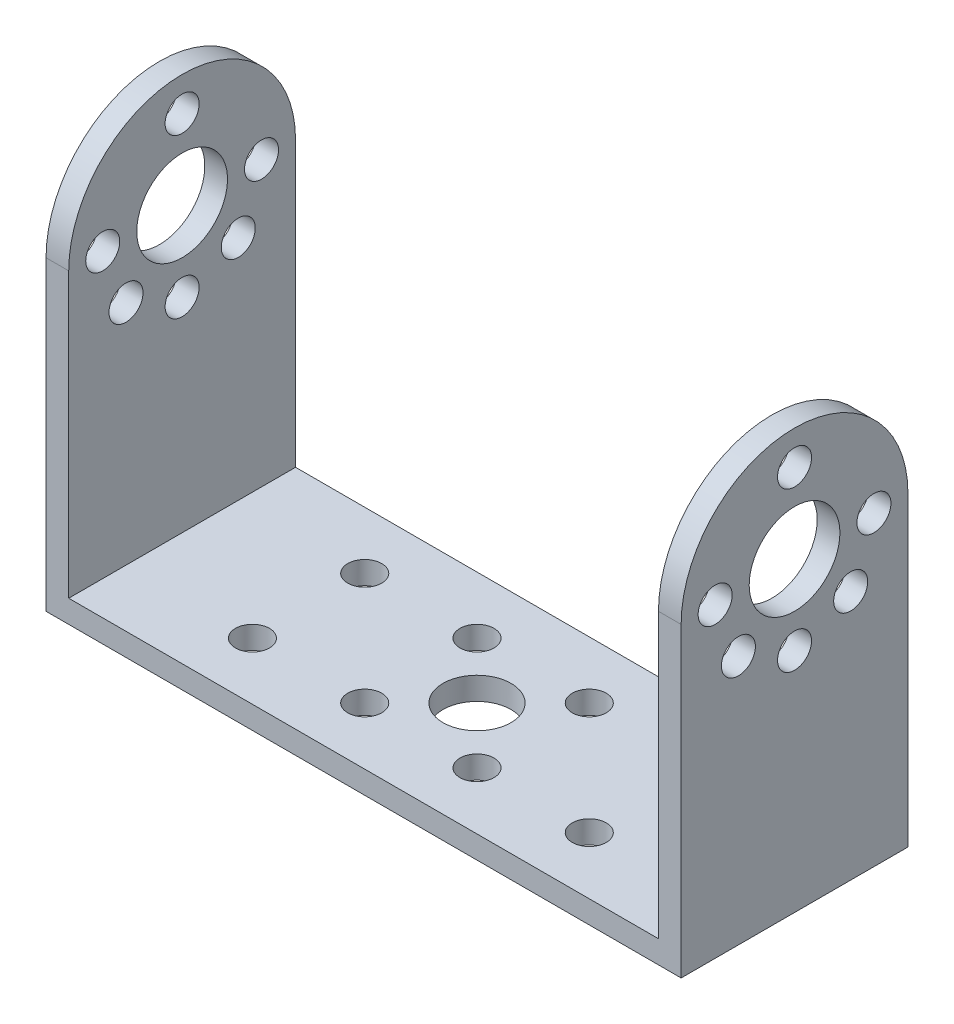
SolidWorks part; units mm, degrees
ref_plane "前视基准面" through (0, 0, 0) normal (0, 0, 1) x (1, 0, 0)
ref_plane "上视基准面" through (0, 0, 0) normal (0, 1, 0) x (1, 0, 0)
ref_plane "右视基准面" through (0, 0, 0) normal (1, 0, 0) x (0, 0, -1)
sketch "草图1" plane through (0, 0, 0) normal (0, 1, 0) x (1, 0, 0)
  line L1 (0, 0) -> (56, 0)
  line L2 (0, 0) -> (0, 20)
  line L3 (0, 20) -> (56, 20)
  line L4 (56, 0) -> (56, 20)
  dimension "D1" = 20
  dimension "D2" = 56
extrude "凸台-拉伸1" add sketch "草图1" along normal blind 2
sketch "草图2" plane through (0, 2, 0) normal (0, 1, 0) x (1, 0, 0)
  line L0 (28, 20) -> (28, 0) construction
  line L1 (56, 20) -> (0, 20) construction
  line L2 (0, 10) -> (56, 10) construction
  line L3 (0, 20) -> (0, 0) construction
  line L4 (56, 0) -> (56, 20) construction
  line L5 (28, 10) -> (35.7612, 2.2388) construction
  line L6 (23.0503, 14.9497) -> (23.0503, 5.0503) construction
  line L7 (18.1005, 10) -> (25.8617, 2.2388) construction
  circle A0 centre (28, 10) radius 3
  circle A1 centre (28, 10) radius 7 construction
  circle A2 centre (32.9497, 5.0503) radius 1.5
  circle A3 centre (23.0503, 5.0503) radius 1.5
  circle A4 centre (23.0503, 14.9497) radius 1.5
  circle A5 centre (32.9497, 14.9497) radius 1.5
  circle A6 centre (18.1005, 10) radius 7 construction
  circle A7 centre (13.1508, 14.9497) radius 1.5
  circle A8 centre (13.1508, 5.0503) radius 1.5
  circle A9 centre (42.8492, 5.0503) radius 1.5
  circle A10 centre (42.8492, 14.9497) radius 1.5
  point P26 (28, 10)
  dimension "D1" = 4
extrude "切除-拉伸1" cut sketch "草图2" against normal up to next
sketch "草图3" plane through (0, 0, 0) normal (-1, 0, 0) x (0, 0, 1)
  line L1 (-20, 2) -> (0, 2)
  line L2 (-20, 2) -> (-20, 27)
  line L4 (0, 2) -> (0, 27)
  arc A0 (0, 27) -> (-20, 27) centre (-10, 27) ccw
  dimension "D5" = 10
  dimension "D1" = 25
  dimension "D2" = 20
  dimension "D3" = 25
  dimension "D4" = 25
extrude "凸台-拉伸2" add sketch "草图3" against normal blind 2
sketch "草图4" plane through (0, 0, 0) normal (-1, 0, 0) x (0, 0, 1)
  circle A0 centre (-10, 27) radius 4
  circle A1 centre (-10, 27) radius 7 construction
  circle A2 centre (-10, 34) radius 1.5
  circle A3 centre (-5.0503, 31.9497) radius 1.5 [skipped]
  circle A4 centre (-3, 27) radius 1.5
  circle A5 centre (-5.0503, 22.0503) radius 1.5
  circle A6 centre (-10, 20) radius 1.5
  circle A7 centre (-14.9497, 22.0503) radius 1.5
  circle A8 centre (-17, 27) radius 1.5
  circle A9 centre (-14.9497, 31.9497) radius 1.5 [skipped]
  point P23 (-10, 27)
  dimension "D1" = 8
  dimension "D2" = 14
extrude "切除-拉伸2" cut sketch "草图4" against normal up to next (2 mm away)
ref_plane "基准面1" through (28, 0, 0) normal (-1, 0, 0) x (0, 0, 1)
mirror "镜向1" about plane through (28, 0, 0) normal (-1, 0, 0) of "凸台-拉伸2", "切除-拉伸2"
